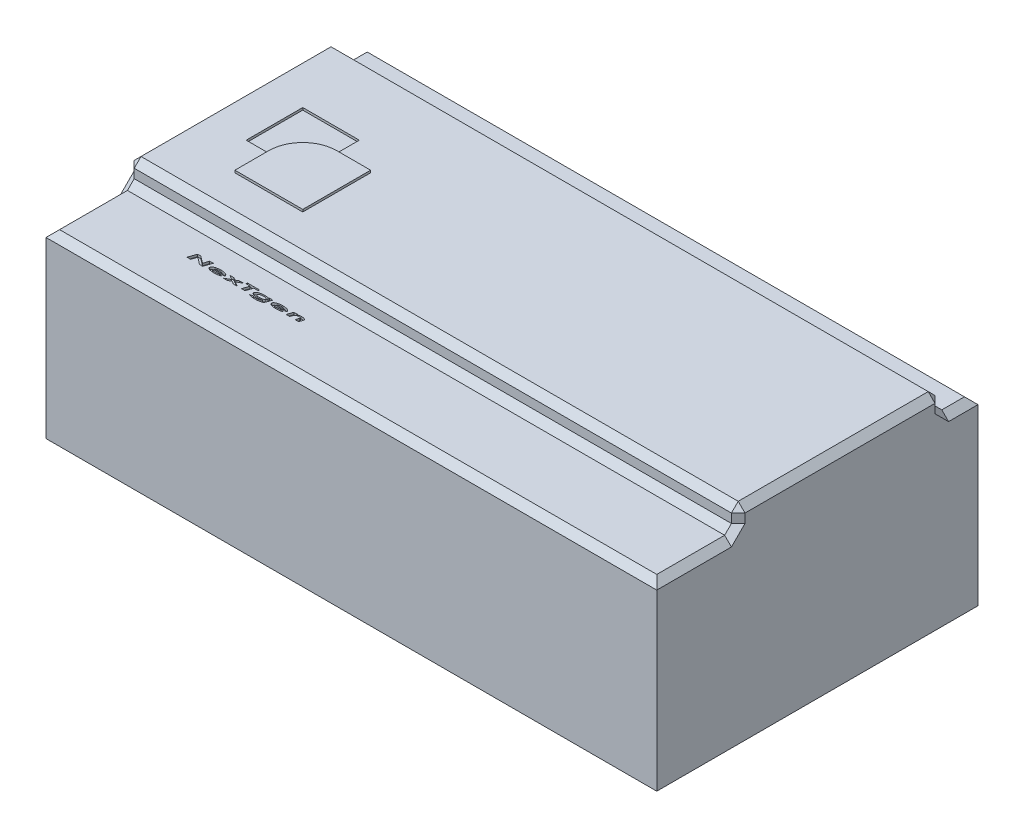
SolidWorks part; units mm, degrees
ref_plane "Front Plane" through (0, 0, 0) normal (0, 0, 1) x (1, 0, 0)
ref_plane "Top Plane" through (0, 0, 0) normal (0, 1, 0) x (1, 0, 0)
ref_plane "Right Plane" through (0, 0, 0) normal (1, 0, 0) x (0, 0, -1)
sketch "Sketch1" plane through (0, 0, 0) normal (0, 1, 0) x (1, 0, 0)
  line L1 (-135, -71) -> (135, -71)
  line L2 (-135, -71) -> (-135, 71)
  line L3 (-135, 71) -> (135, 71)
  line L4 (135, -71) -> (135, 71)
  line L5 (-135, -71) -> (135, 71) construction
  line L6 (-135, 71) -> (135, -71) construction
  point P0 (0, 0)
  dimension "D1" = 142
  dimension "D2" = 270
extrude "Boss-Extrude1" add sketch "Sketch1" along normal blind 80
sketch "Sketch2" plane through (0, 80, 0) normal (0, 1, 0) x (1, 0, 0)
  line L0 (135, -71) -> (135, 71) construction
  line L1 (-135, -35) -> (135, -35)
  line L2 (-135, -35) -> (-135, 35)
  line L4 (135, -35) -> (135, 35)
  line L5 (-135, -35) -> (135, 35) construction
  line L6 (-135, 35) -> (135, -35) construction
  line L9 (-135, 35) -> (-135, 55)
  line L10 (-135, 55) -> (135, 55)
  line L11 (135, 35) -> (135, 55)
  point P0 (0, 0)
  dimension "D1" = 70
  dimension "D2" = 20
extrude "Boss-Extrude2" add sketch "Sketch2" along normal blind 10
sketch "Sketch6" plane through (-135, 0, 0) normal (-1, 0, 0) x (0, 0, 1)
  circle A0 centre (-24.4276, 39.9049) radius 5
  circle A1 centre (22.5185, 39.9049) radius 5
  dimension "D1" = 10
  dimension "D2" = 10
extrude "Boss-Extrude5" add sketch "Sketch6" along normal blind 2
sketch "Sketch7" plane through (0, 80, 0) normal (0, 1, 0) x (1, 0, 0)
  text T0 "<b><i>NexTgen</i></b>" font "Century Gothic" height 3.5
extrude "Cut-Extrude2" cut sketch "Sketch7" against normal blind 1
chamfer "Chamfer1" distance 3 angle 45 16 edges at (0, 80, 71) (0, 80, 35) (0, 90, 35) (0, 90, -55) (0, 80, -55) (0, 80, -71) (135, 80, -63) (135, 85, -55) (135, 90, -10) (135, 85, 35) (135, 80, 53) (-135, 80, 53) (-135, 85, 35) (-135, 90, -10) (-135, 85, -55) (-135, 80, -63)
sketch "Sketch8" plane through (0, 90, 0) normal (0, 1, 0) x (1, 0, 0)
  line L0 (-135, -32) -> (-135, 52) construction
  line L1 (-115, -2.5) -> (-90, -2.5)
  line L2 (-115, -2.5) -> (-115, 22.5)
  line L3 (-115, 22.5) -> (-90, 22.5)
  line L4 (-90, -2.5) -> (-90, 22.5)
  line L5 (-115, -2.5) -> (-90, 22.5) construction
  line L6 (-115, 22.5) -> (-90, -2.5) construction
  line L7 (132, 55) -> (-132, 55) construction
  point P0 (-102.5, 10)
  dimension "D1" = 25
  dimension "D2" = 25
  dimension "D3" = 20
  dimension "D4" = 45
extrude "Cut-Extrude3" cut sketch "Sketch8" against normal blind 1
sketch "Sketch9" plane through (0, 90, 0) normal (0, 1, 0) x (1, 0, 0)
  line L1 (-90, 12.5) -> (-75, 12.5)
  line L2 (-105, -2.5) -> (-105, -17.5)
  line L3 (-105, -17.5) -> (-75, -17.5)
  line L4 (-75, 12.5) -> (-75, -17.5)
  line L5 (-105, 12.5) -> (-75, -17.5) construction
  line L6 (-105, -17.5) -> (-75, 12.5) construction
  arc A0 (-90, 12.5) -> (-105, -2.5) centre (-90, -2.5) ccw
  point P0 (-90, -2.5)
  dimension "D3" = 15
  dimension "D1" = 30
  dimension "D2" = 30
extrude "Boss-Extrude6" add sketch "Sketch9" along normal blind 1
